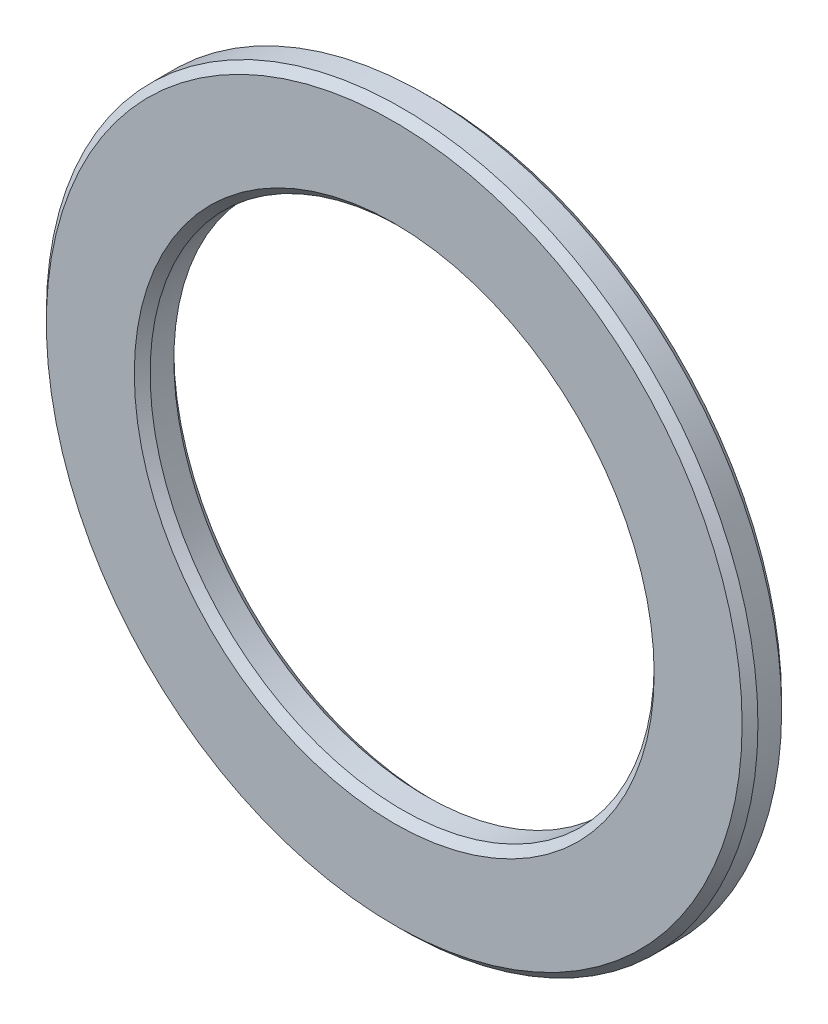
SolidWorks part; units mm, degrees
ref_plane "Front Plane" through (0, 0, 0) normal (0, 0, 1) x (1, 0, 0)
ref_plane "Top Plane" through (0, 0, 0) normal (0, 1, 0) x (1, 0, 0)
ref_plane "Right Plane" through (0, 0, 0) normal (1, 0, 0) x (0, 0, -1)
sketch "Sketch1" plane through (0, 0, 0) normal (0, 0, 1) x (1, 0, 0)
  circle A0 centre (0, 0) radius 12.75
  circle A1 centre (0, 0) radius 18
  dimension "D1" = 25.5
  dimension "D2" = 36
extrude "Boss-Extrude1" add sketch "Sketch1" along normal mid plane 2
chamfer "Chamfer1" distance 0.4 angle 45 4 edges at (18, 0, -1) (18, 0, 1) (12.75, 0, -1) (12.75, 0, 1)
